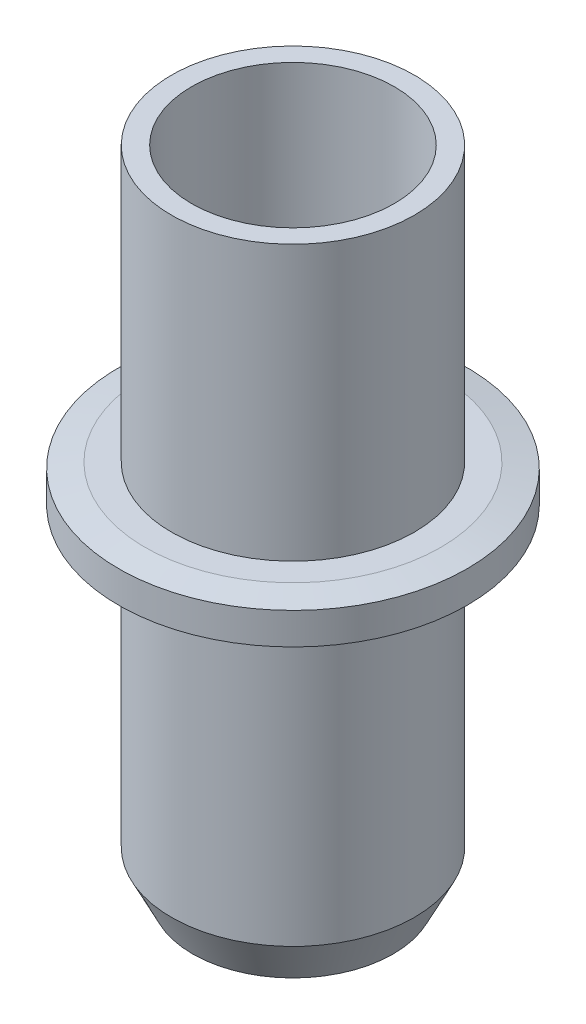
SolidWorks part; units mm, degrees
ref_plane "Front Plane" through (0, 0, 0) normal (0, 0, 1) x (1, 0, 0)
ref_plane "Top Plane" through (0, 0, 0) normal (0, 1, 0) x (1, 0, 0)
ref_plane "Right Plane" through (0, 0, 0) normal (1, 0, 0) x (0, 0, -1)
sketch "Sketch1" plane through (0, 0, 0) normal (0, 0, 1) x (1, 0, 0)
  line L0 (0, -143.9505) -> (0, 7053.5726) construction
  line L1 (0, 0) -> (2.375, 0)
  line L2 (2.375, 0) -> (3.2, 5.5)
  line L3 (3.2, 5.5) -> (3.2, 6.5)
  line L4 (3.2, 6.5) -> (4.75, 6.5)
  line L5 (4.75, 6.5) -> (5.75, 8.5)
  line L6 (5.75, 8.5) -> (5.75, 22.3)
  line L7 (5.75, 22.3) -> (7, 22.3)
  line L8 (7, 22.3) -> (8.25, 22.55)
  line L9 (8.25, 22.55) -> (8.25, 24.05)
  line L10 (8.25, 24.05) -> (7, 24.3)
  line L11 (7, 24.3) -> (5.75, 24.3)
  line L12 (5.75, 24.3) -> (5.75, 37.3)
  line L13 (5.75, 37.3) -> (0, 37.3)
  line L14 (0, 37.3) -> (0, 0)
  point P18 (0, 37.3)
  point P29 (0, 0)
  dimension "D2" = 15.8
  dimension "D3" = 11.5
  dimension "D4" = 2
  dimension "D5" = 1.5
  dimension "D6" = 16.5
  dimension "D7" = 6.5
  dimension "D8" = 1
  dimension "D9" = 6.4
  dimension "D10" = 4.75
  dimension "D11" = 2
  dimension "D12" = 1.25
  dimension "D13" = 13
  dimension "D14" = 9.5
revolve "5.63 mm bottom to pen tip" add sketch "Sketch1" angle 360 about L0
sketch "Sketch2" plane through (0, 0, 0) normal (0, 0, 1) x (1, 0, 0)
  line L0 (0, -1000) -> (0, 49000) construction
  line L1 (0, -5.63) -> (0.39, -5.63)
  line L2 (0.39, -5.63) -> (0.39, -2.03)
  line L3 (0.39, -2.03) -> (1.1, -2.03)
  line L4 (1.1, -2.03) -> (1.65, 0.35)
  line L5 (1.65, 0.35) -> (2.4, 0.35)
  line L6 (2.4, 0.35) -> (4.185, 10.48)
  line L7 (4.185, 10.48) -> (4.8, 10.48)
  line L8 (4.8, 10.48) -> (4.8, 42.48)
  line L9 (4.8, 42.48) -> (5.9674, 42.48)
  line L10 (5.9674, 42.48) -> (5.9674, 45.0515)
  line L11 (5.9674, 45.0515) -> (0, 45.0515)
  line L12 (-2.375, 0) -> (2.375, 0) construction
  line L13 (0, -5.63) -> (0, 45.0515)
  dimension "D1" = 0.78
  dimension "D2" = 3.6
  dimension "D3" = 2.2
  dimension "D4" = 2.38
  dimension "D5" = 3.3
  dimension "D6" = 4.8
  dimension "D7" = 8.37
  dimension "D8" = 9.6
  dimension "D9" = 10.13
  dimension "D10" = 5.63
  dimension "D11" = 32
revolve "Cut-Revolve1" cut sketch "Sketch2" angle 360 about L0
